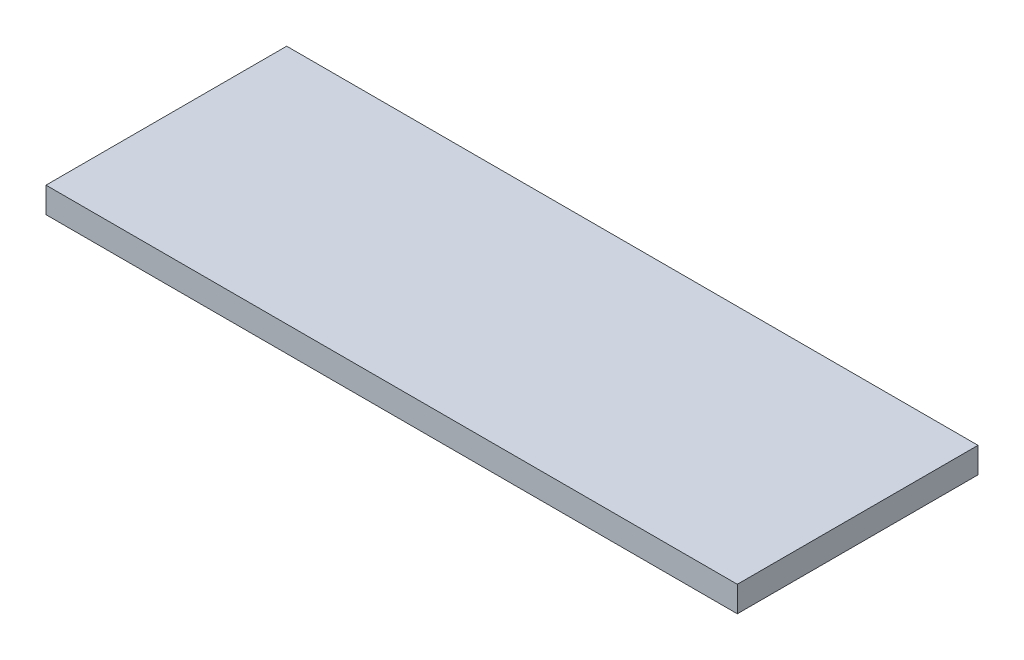
SolidWorks part; units mm, degrees
ref_plane "Front Plane" through (0, 0, 0) normal (0, 0, 1) x (1, 0, 0)
ref_plane "Top Plane" through (0, 0, 0) normal (0, 1, 0) x (1, 0, 0)
ref_plane "Right Plane" through (0, 0, 0) normal (1, 0, 0) x (0, 0, -1)
sketch "Sketch1" plane through (0, 0, 0) normal (0, 1, 0) x (1, 0, 0)
  line L1 (-81, 28.2) -> (81, 28.2)
  line L2 (-81, 28.2) -> (-81, -28.2)
  line L3 (-81, -28.2) -> (81, -28.2)
  line L4 (81, 28.2) -> (81, -28.2)
  line L5 (-81, 28.2) -> (81, -28.2) construction
  line L6 (-81, -28.2) -> (81, 28.2) construction
  point P0 (0, 0)
  dimension "D2" = 56.4
  dimension "D1" = 162
sketch "Sketch2" plane through (0, 0, 0) normal (0, 0, 1) x (1, 0, 0)
  line L0 (0, 0) -> (0, 6) construction
  line L1 (-81, 0) -> (81, 0) construction
  point P4 (0, 0)
  dimension "D1" = 6
extrude "Boss-Extrude1" add sketch "Sketch1" along normal up to vertex (6 mm away) contours L2 L3 L4 L1 up to point (0, 6, 0)
equation "\"glass_width\" = 150"
equation "\"glass_height\"= 100"
equation "\"glass_thickness\"= 4"
equation "\"brood_space\"= 42"
equation "\"t1\"= 6"
equation "\"t2\"= 3.2"
equation "\"box_depth\"= \"brood_space\" + \"glass_thickness\" + \"glass_thickness\" + \"t2\" + \"t2\""
equation "\"box_width\"= \"glass_width\" + \"t1\" + \"t1\""
equation "\"food_height\"= 70"
equation "\"box_height\" = \"glass_height\" + ( \"t1\" * 3 ) + \"food_height\""
equation "\"D1@Sketch1\"=\"box_width\""
equation "\"D2@Sketch1\"=\"box_depth\""
equation "\"D1@Sketch2\"=\"t1\""
